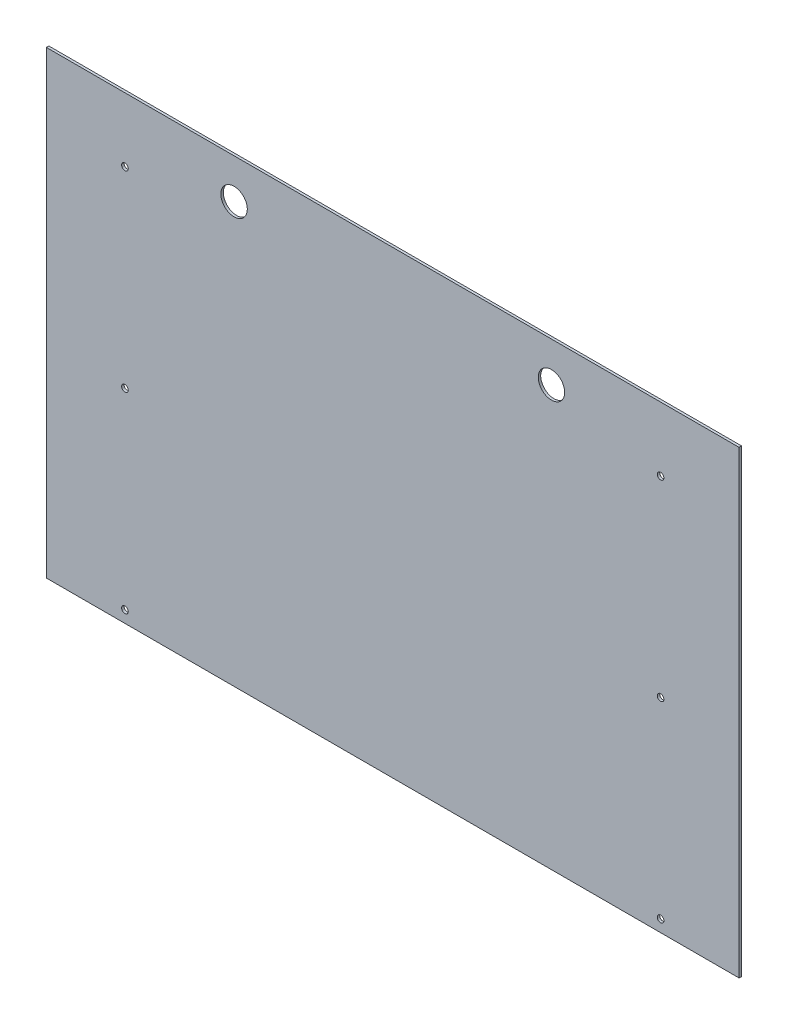
SolidWorks part; units mm, degrees
material "Perspex (TM) GS Acrylic Cast Sheet"
ref_plane "Front Plane" through (0, 0, 0) normal (0, 0, 1) x (1, 0, 0)
ref_plane "Top Plane" through (0, 0, 0) normal (0, 1, 0) x (1, 0, 0)
ref_plane "Right Plane" through (0, 0, 0) normal (1, 0, 0) x (0, 0, -1)
sketch "Sketch1" plane through (0, 0, 0) normal (0, 0, 1) x (1, 0, 0)
  line L0 (665.1625, 1079.5) -> (665.1625, 196.85) construction
  line L1 (-665.1625, 1079.5) -> (665.1625, 1079.5)
  line L2 (-665.1625, 1079.5) -> (-665.1625, 196.85)
  line L3 (-665.1625, 196.85) -> (665.1625, 196.85)
  line L4 (665.1625, 1079.5) -> (665.1625, 196.85)
  line L5 (660.4, 196.85) -> (-660.4, 196.85) construction
  line L10 (0, 0) -> (0, 1079.5) construction
  line L11 (488.95, 1117.6) -> (539.75, 1117.6) construction
  dimension "D1" = 38.1
extrude "Extrude1" add sketch "Sketch1" along normal blind 4.7625
sketch "Sketch2" plane through (0, 0, 4.7625) normal (0, 0, 1) x (1, 0, 0)
  line L0 (514.35, 958.85) -> (514.35, 956.31) construction
  line L3 (514.35, 590.55) -> (514.35, 588.01) construction
  line L4 (514.35, 222.25) -> (514.35, 219.71) construction
  line L5 (0, 0) -> (0, 1473.4644) construction
  line L6 (0, 0) -> (0, 1517.5653) construction
  line L7 (-514.35, 222.25) -> (-514.35, 219.71) construction
  line L8 (-514.35, 590.55) -> (-514.35, 588.01) construction
  line L9 (-514.35, 958.85) -> (-514.35, 956.31) construction
  circle A0 centre (514.35, 956.31) radius 6.35
  circle A2 centre (514.35, 958.85) radius 6.35 construction
  circle A4 centre (514.35, 588.01) radius 6.35
  circle A6 centre (514.35, 219.71) radius 6.35
  circle A7 centre (-514.35, 219.71) radius 6.35
  circle A8 centre (-514.35, 588.01) radius 6.35
  circle A9 centre (-514.35, 956.31) radius 6.35
  dimension "D1" = 2.54
extrude "Cut-Extrude1" cut sketch "Sketch2" against normal through all
sketch "Sketch3" plane through (0, 0, 4.7625) normal (0, 0, 1) x (1, 0, 0)
  line L0 (0, 1079.5) -> (0, 600.0109) construction
  line L1 (665.1625, 1079.5) -> (-665.1625, 1079.5) construction
  circle A0 centre (304.8, 1003.3) radius 25.4
  circle A1 centre (-304.8, 1003.3) radius 25.4
  dimension "D3" = 50.8
  dimension "D1" = 609.6
  dimension "D2" = 76.2
extrude "Cut-Extrude2" cut sketch "Sketch3" against normal through all
